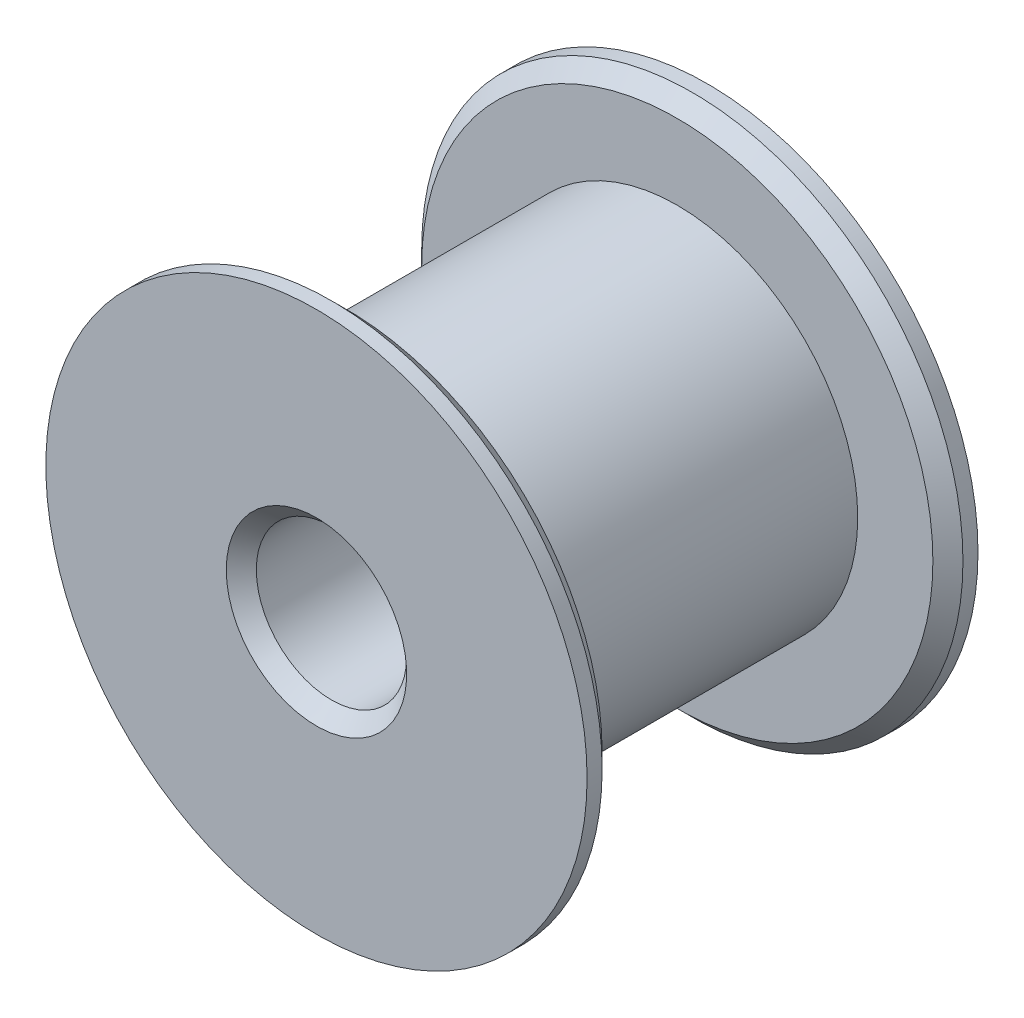
SolidWorks part; units mm, degrees
material "1023 Carbon Steel Sheet (SS)"
ref_plane "Front Plane" through (0, 0, 0) normal (0, 0, 1) x (1, 0, 0)
ref_plane "Top Plane" through (0, 0, 0) normal (0, 1, 0) x (1, 0, 0)
ref_plane "Right Plane" through (0, 0, 0) normal (1, 0, 0) x (0, 0, -1)
sketch "Sketch1" plane through (0, 0, 0) normal (0, 1, 0) x (1, 0, 0)
  line L0 (0, 6.5) -> (-2.5, 6.5) construction
  line L2 (0, 0) -> (0, 13) construction
  line L5 (-2.5, 0) -> (-2.5, 13)
  line L6 (-2.5, 13) -> (-9, 13)
  line L7 (-9, 13) -> (-9, 12)
  line L8 (-9, 0) -> (-2.5, 0)
  line L9 (-9, 1) -> (-6, 1)
  line L10 (-6, 1) -> (-6, 12)
  line L11 (-6, 12) -> (-9, 12)
  line L12 (-9, 1) -> (-9, 0)
  point P7 (-2.5, 6.5)
  dimension "D1" = 13
  dimension "D2" = 2.5
  dimension "D3" = 9
  dimension "D4" = 1
  dimension "D5" = 1
  dimension "D6" = 6
revolve "Revolve1" add sketch "Sketch1" angle 360 about L2
chamfer "Chamfer1" distance 0.5 angle 45 4 edges at (2.5, 0, -13) (2.5, 0, 0) (9, 0, -12) (9, 0, -1)
